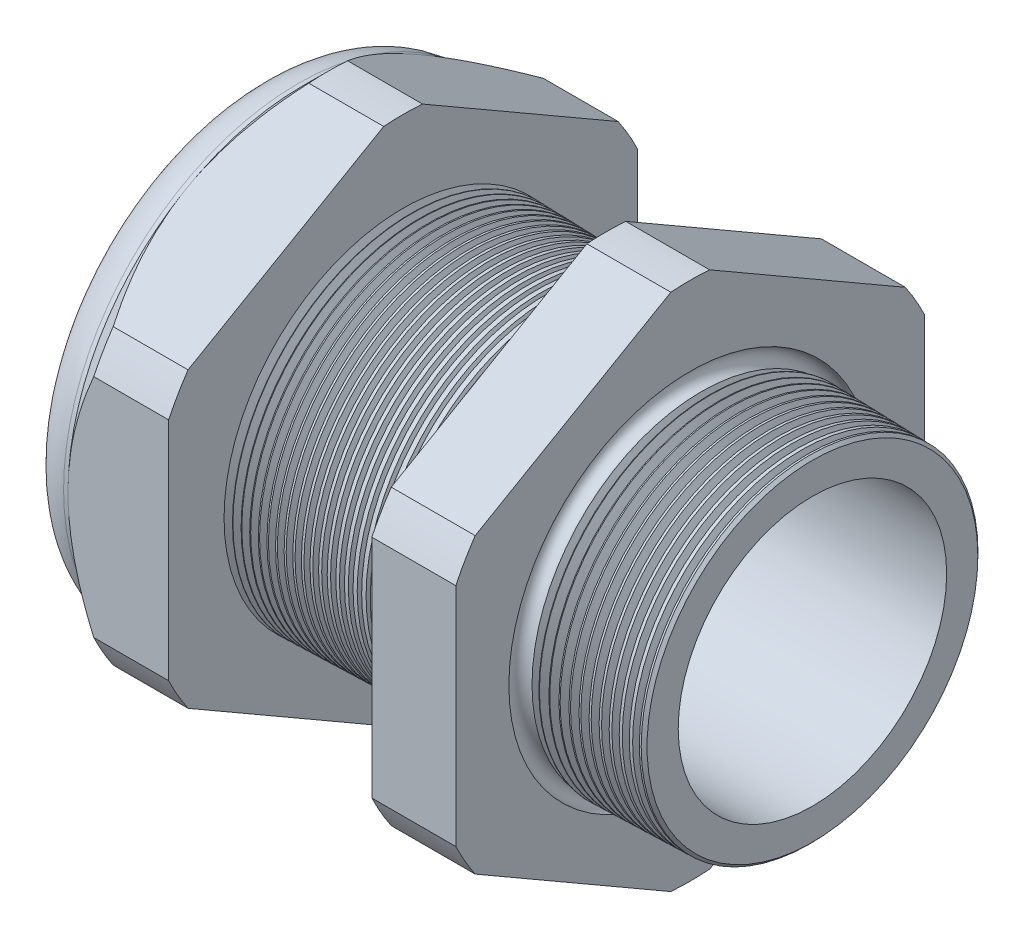
SolidWorks part; units mm, degrees
ref_plane "Front Plane" through (0, 0, 0) normal (0, 0, 1) x (1, 0, 0)
ref_plane "Top Plane" through (0, 0, 0) normal (0, 1, 0) x (1, 0, 0)
ref_plane "Right Plane" through (0, 0, 0) normal (1, 0, 0) x (0, 0, -1)
sketch "Sketch10" plane through (0, 0, 0) normal (0, 0, 1) x (1, 0, 0)
  line L0 (0, 0) -> (-115.3565, 0) construction
  line L1 (-46.736, 12.446) -> (-33.536, 12.446)
  line L2 (3.048, 11.996) -> (3.048, 15.044)
  line L3 (-7.874, 15.33) -> (3.048, 15.044)
  line L4 (-7.874, 41.91) -> (-7.874, 15.33)
  line L5 (-7.874, 41.91) -> (-15.374, 41.91)
  line L6 (-15.374, 41.91) -> (-15.374, 15.5264)
  line L7 (-33.536, 16.002) -> (-15.374, 15.5264)
  line L8 (-33.536, 16.002) -> (-33.536, 41.91)
  line L9 (-33.536, 41.91) -> (-42.536, 41.91)
  line L10 (-42.536, 41.91) -> (-42.536, 20.955)
  line L11 (-42.536, 20.955) -> (-46.736, 20.955)
  line L12 (-46.736, 20.955) -> (-46.736, 12.446)
  line L13 (-33.536, 12.446) -> (3.048, 11.996)
  dimension "D1" = 49.784
  dimension "D2" = 24.892
  dimension "D3" = 1.5
  dimension "D4" = 3.048
  dimension "A" = 32.004
  dimension "D6" = 41.91
  dimension "D8" = 83.82
  dimension "D9" = 4.2
  dimension "D10" = 9
  dimension "D11" = 7.5
  dimension "D" = 10.922
revolve "Revolve2" add sketch "Sketch10" angle 360 about L0
sketch "Sketch12" plane through (-42.536, 0, 0) normal (-1, 0, 0) x (0, 0, 1)
  line L1 (-1.7346, 23.1953) -> (-19.2204, 13.0998)
  line L2 (-20.955, 10.0954) -> (-20.955, -10.0954)
  line L3 (-19.2204, -13.0998) -> (-1.7346, -23.1953)
  line L4 (1.7346, -23.1953) -> (19.2204, -13.0998)
  line L5 (20.955, -10.0954) -> (20.955, 10.0954)
  line L6 (19.2204, 13.0998) -> (1.7346, 23.1953)
  circle A0 centre (0, 0) radius 20.955 construction
  arc A1 (1.7346, 23.1953) -> (-1.7346, 23.1953) centre (0, 0) ccw
  arc A2 (-19.2204, 13.0998) -> (-20.955, 10.0954) centre (0, 0) ccw
  arc A3 (-20.955, -10.0954) -> (-19.2204, -13.0998) centre (0, 0) ccw
  arc A4 (-1.7346, -23.1953) -> (1.7346, -23.1953) centre (0, 0) ccw
  arc A5 (19.2204, -13.0998) -> (20.955, -10.0954) centre (0, 0) ccw
  arc A6 (20.955, 10.0954) -> (19.2204, 13.0998) centre (0, 0) ccw
  dimension "D2" = 46.5201
  dimension "D1" = 41.91
extrude "Cut-Extrude2" cut sketch "Sketch12" against normal through all flip side to cut
fillet "Fillet4" radius 3.81 1 edges at (-46.736, 0, -20.955)
sketch "Sketch19" plane through (-42.536, 0, 0) normal (-1, 0, 0) x (0, 0, 1)
  line L0 (20.955, 0) -> (20.955, 10.0954) construction
  circle A0 centre (0, 0) radius 20.955
extrude "Cut-Extrude3" cut sketch "Sketch19" against normal blind 3.998 draft 45 flip side to cut
chamfer "Chamfer1" distance 0.254 angle 45 1 edges at (3.048, 0, -15.044)
sketch "Sketch21" plane through (-46.736, 0, 0) normal (-1, 0, 0) x (0, 0, 1)
  circle A0 centre (0, 0) radius 12.446
  circle A2 centre (0, 0) radius 12.446 construction
extrude "plug" add sketch "Sketch21" against normal blind 12.7 separate body
sketch "Sketch22" plane through (-46.736, 0, 0) normal (-1, 0, 0) x (0, 0, 1)
  circle A0 centre (0, 0) radius 12.192
  circle A1 centre (0, 0) radius 12.446 construction
  dimension "D1" = 0.254
extrude "Cut-Extrude4" cut sketch "Sketch22" against normal blind 0.508
sketch "Sketch27" plane through (-46.228, 0, 0) normal (-1, 0, 0) x (0, 0, 1)
  line L0 (-4.3624, 0) -> (4.3624, 0) construction
  circle A0 centre (-7.4742, 0) radius 4.699
  circle A1 centre (0, 0) radius 12.192 construction
  dimension "D1" = 0.0188
  dimension "holedia" = 9.398
extrude "plugholes" cut sketch "Sketch27" against normal through all
pattern_circular "CirPattern1" count 4 over 360 about axis through (0, 0, 0) along (1, 0, 0) of "plugholes"
sketch "Sketch28" [suppressed] plane through (-29.464, 0, 0) normal (-1, 0, 0) x (0, 0, 1)
  circle A0 centre (0, 0) radius 0.762
  dimension "midholedia" = 9.398
extrude "midhole" [suppressed] cut sketch "Sketch28" against normal through all
sketch "Sketch29" plane through (0, 0, 0) normal (0, 0, 1) x (1, 0, 0)
  line L0 (-33.536, 16.002) -> (-32.803, 15.9828)
  line L1 (-15.374, 15.5264) -> (-33.536, 16.002) construction
  line L2 (-32.803, 15.9828) -> (-33.1861, 15.3576)
  line L3 (-33.1861, 15.3576) -> (-33.536, 16.002)
  dimension "D1" = 60
  dimension "D2" = 60
  dimension "D3" = 0.635
revolve "Cut-Revolve1" cut sketch "Sketch29" angle 360 about axis through (0, 0, 0) along (-1, 0, 0)
pattern_linear "LPattern1" count 24 spacing 0.762 along (1, 0, 0) of "Cut-Revolve1"
sketch "Sketch30" plane through (0, 0, 0) normal (0, 0, 1) x (1, 0, 0)
  line L0 (-7.874, 15.33) -> (-6.9944, 15.307)
  line L1 (-7.874, 23.1953) -> (-7.874, 13.0998) construction
  line L2 (2.7941, 15.0507) -> (-7.874, 15.33) construction
  line L3 (-6.9944, 15.307) -> (-7.4542, 14.5568)
  line L4 (-7.4542, 14.5568) -> (-7.874, 15.33)
  dimension "D1" = 60
  dimension "D2" = 60
  dimension "D3" = 0.762
revolve "Cut-Revolve2" cut sketch "Sketch30" angle 360 about axis through (0, 0, 0) along (-1, 0, 0)
pattern_linear "LPattern2" count 12 spacing 0.889 along (1, 0, 0) of "Cut-Revolve2"
sketch "Sketch31" [suppressed] plane through (-38.354, 0, 0) normal (-1, 0, 0) x (0, 0, 1)
  line L0 (-1.905, 1.905) -> (1.905, 1.905)
  line L1 (-1.905, -1.905) -> (1.905, -1.905)
  circle A0 centre (0, 0) radius 1.905 construction
  arc A1 (-1.905, 1.905) -> (-1.905, -1.905) centre (-1.905, 0) ccw
  arc A2 (1.905, 1.905) -> (1.905, -1.905) centre (1.905, 0) cw
extrude "Cut-Extrude5" [suppressed] cut sketch "Sketch31" against normal through all
sketch "Sketch32" plane through (0, 0, 0) normal (0, 0, 1) x (1, 0, 0)
  line L0 (-7.874, 23.1953) -> (-7.874, 13.0998) construction
  circle A0 centre (-7.747, 15.33) radius 0.889
  dimension "D2" = 1.778
  dimension "D1" = 0.127
revolve "Cut-Revolve3" cut sketch "Sketch32" angle 360 about axis through (0, 0, 0) along (-1, 0, 0)
